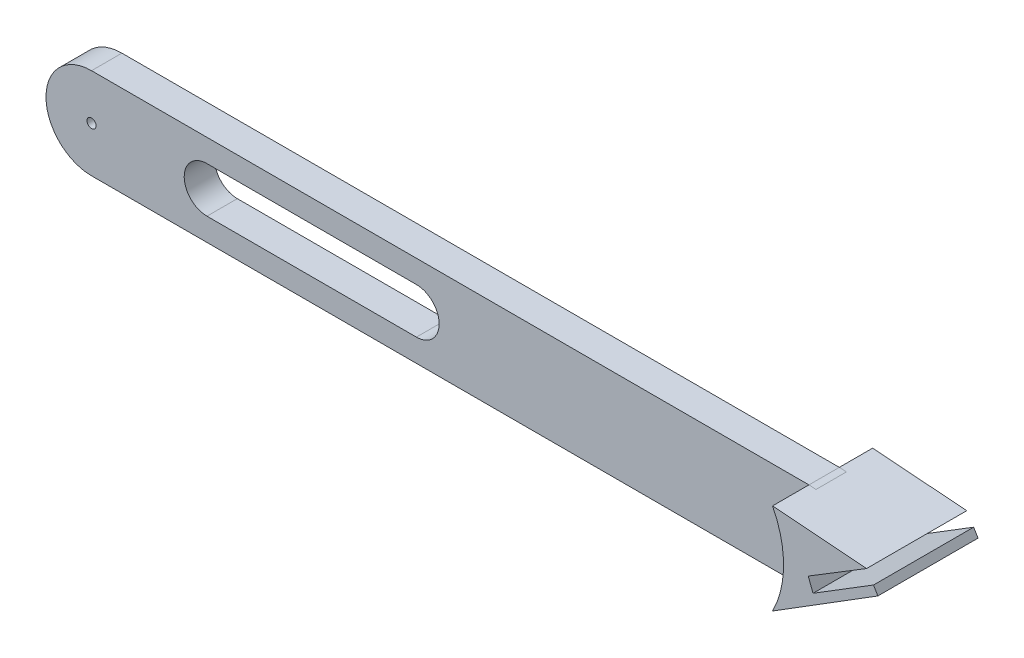
SolidWorks part; units mm, degrees
ref_plane "前视基准面" through (0, 0, 0) normal (0, 0, 1) x (1, 0, 0)
ref_plane "上视基准面" through (0, 0, 0) normal (0, 1, 0) x (1, 0, 0)
ref_plane "右视基准面" through (0, 0, 0) normal (1, 0, 0) x (0, 0, -1)
sketch "草图1" plane through (0, 0, 0) normal (0, 0, 1) x (1, 0, 0)
  line L0 (-14, 5.976) -> (64.7841, 5.976) construction
  line L1 (-14, 10.976) -> (64.7841, 10.976)
  line L2 (-14, 0.976) -> (64.7841, 0.976)
  line L5 (21.6763, 5.976) -> (-1.3237, 5.976) construction
  line L6 (21.6763, 3.476) -> (-1.3237, 3.476)
  line L7 (21.6763, 8.476) -> (-1.3237, 8.476)
  arc A0 (-14, 10.976) -> (-14, 0.976) centre (-14, 5.976) ccw
  arc A1 (64.7841, 0.976) -> (64.7841, 10.976) centre (64.7841, 5.976) ccw
  arc A2 (21.6763, 3.476) -> (21.6763, 8.476) centre (21.6763, 5.976) ccw
  arc A3 (-1.3237, 8.476) -> (-1.3237, 3.476) centre (-1.3237, 5.976) ccw
  point P2 (25.3921, 5.976)
  point P7 (0, 0)
  point P9 (10.1763, 5.976)
  point P15 (-1.3237, 4.9245)
  point P16 (0, 0)
  point P17 (64.7841, 5.976)
  dimension "D1" = 2.5
  dimension "D2" = 5
  dimension "D3" = 23
extrude "凸台-拉伸1" add sketch "草图1" along normal blind 1.4 and the other way blind 1.935
ref_point "点1"
hole_wizard "大小mm 暗销孔1" positions "草图4" profile "草图5" hole size "Ø1.0" standard "ISO"
sketch "草图4" plane through (0, 0, -1.935) normal (0, 0, -1) x (-1, 0, 0)
  point P0 (14, 5.976)
sketch "草图5" plane through (-14, 5.976, -1.935) normal (1, 0, 0) x (0, 1, 0)
  line L0 (0, 0) -> (0, 4)
  line L1 (0, 4) -> (0.5, 3.6996)
  line L2 (0.5, 3.6996) -> (0.5, 0)
  line L5 (0.5, 0) -> (0, 0)
  line L10 (0, 4) -> (-0.5, 3.6996) construction
  line L11 (0, -6.35) -> (0, 107.95) construction
  dimension "孔直径" = 1
  dimension "孔深度" = 4
  dimension "导头角度" = 118
ref_point "点2"
hole_wizard "大小mm 暗销孔2" positions "草图6" profile "草图7" hole size "Ø1.0" standard "ISO"
sketch "草图6" plane through (0, 0, -1.935) normal (0, 0, -1) x (-1, 0, 0)
  point P0 (-64.7841, 5.976)
sketch "草图7" plane through (64.7841, 5.976, -1.935) normal (1, 0, 0) x (0, 1, 0)
  line L0 (0, 0) -> (0, 4)
  line L1 (0, 4) -> (0.5, 3.6996)
  line L2 (0.5, 3.6996) -> (0.5, 0)
  line L5 (0.5, 0) -> (0, 0)
  line L10 (0, 4) -> (-0.5, 3.6996) construction
  line L11 (0, -6.35) -> (0, 107.95) construction
  dimension "孔直径" = 1
  dimension "孔深度" = 4
  dimension "导头角度" = 118
sketch "草图11" plane through (0, 0, 1.4) normal (0, 0, 1) x (1, 0, 0)
  line L1 (64.7841, 10.976) -> (75.1103, 10.1819)
  line L2 (68.7065, 6.2656) -> (75.1103, 10.1819)
  line L3 (64.7841, 0.976) -> (76.3488, 8.1899)
  line L4 (76.3488, 8.1899) -> (75.8768, 9.0013)
  line L5 (75.8768, 9.0013) -> (69.2311, 4.8899)
  line L6 (69.2311, 4.8899) -> (68.7065, 6.2656)
  arc A0 (64.7841, 10.976) -> (64.7841, 0.976) centre (55.0947, 5.976) cw
  point P7 (66.63, 6.3661)
  point P15 (66.8706, 6.3661)
  point P16 (67.367, 7.1947)
  point P17 (69.2311, 5.976)
  point P18 (75.3668, 9.8215)
  point P19 (76.5529, 0.976)
  point P20 (75.5285, 7.6799)
  point P21 (76.3488, 8.1899)
  point P22 (75.8768, 9.0013)
  point P23 (69.2311, 4.8899)
  point P24 (0, 0)
  point P25 (70.2935, 7.1706)
  point P26 (68.7065, 6.2656)
  point P28 (0, 0)
  point P29 (75.0108, 10.1851)
  point P30 (75.1103, 10.1819)
  point P31 (69.7345, 6.542)
extrude "凸台-拉伸4" add sketch "草图11" along normal blind 4 and the other way blind 7
sketch "草图12" plane through (0, 0, 1.4) normal (0, 0, 1) x (1, 0, 0)
  line L0 (69.7027, 6.8749) -> (68.7065, 6.2656)
  line L1 (68.7065, 6.2656) -> (69.2311, 4.8899)
  line L2 (69.2311, 4.8899) -> (69.7226, 5.1939)
  line L3 (69.7226, 5.1939) -> (71.1968, 6.106)
  line L4 (71.1968, 6.106) -> (69.7027, 6.8749)
  line L5 (64.7841, 0.976) -> (69.2747, 3.7771)
  line L6 (69.2747, 3.7771) -> (71.0003, 3.2007)
  line L7 (71.0003, 3.2007) -> (64.1955, -1.2526)
  line L8 (64.1955, -1.2526) -> (64.7841, 0.976)
extrude "切除-拉伸4" cut sketch "草图12" against normal blind 4
